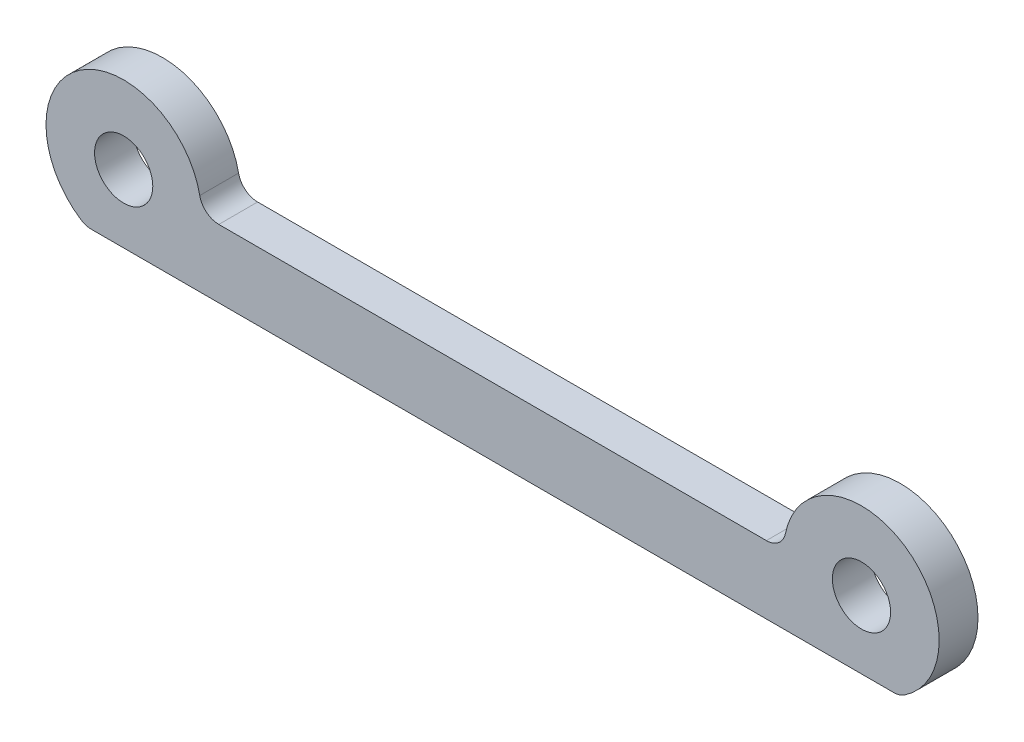
SolidWorks part; units mm, degrees
ref_plane "Alzado" through (0, 0, 0) normal (0, 0, 1) x (1, 0, 0)
ref_plane "Planta" through (0, 0, 0) normal (0, 1, 0) x (1, 0, 0)
ref_plane "Vista lateral" through (0, 0, 0) normal (1, 0, 0) x (0, 0, -1)
sketch "Croquis1" plane through (0, 0, 0) normal (0, 0, 1) x (1, 0, 0)
  line L0 (0, -38.3293) -> (0, 38.3293) construction
  line L1 (15, 3.5) -> (-15, 3.5)
  line L2 (-20.9365, 0) -> (20.9365, 0)
  circle A0 centre (-19, 3.5) radius 1.5
  arc A1 (-15, 3.5) -> (-20.9365, 0) centre (-19, 3.5) ccw
  arc A2 (15, 3.5) -> (20.9365, 0) centre (19, 3.5) cw
  circle A3 centre (19, 3.5) radius 1.5
  point P6 (0, 0)
  point P11 (0, 0)
  point P12 (0, 0)
  point P14 (0, 3.5)
  dimension "D1" = 3.5
  dimension "D2" = 4
  dimension "D4" = 3
  dimension "D3" = 38
extrude "Saliente-Extruir1" add sketch "Croquis1" along normal blind 2
fillet "Redondeo1" radius 1 4 edges at (-20.9365, 0, 1) (20.9365, 0, 1) (15, 3.5, 1) (-15, 3.5, 1)
